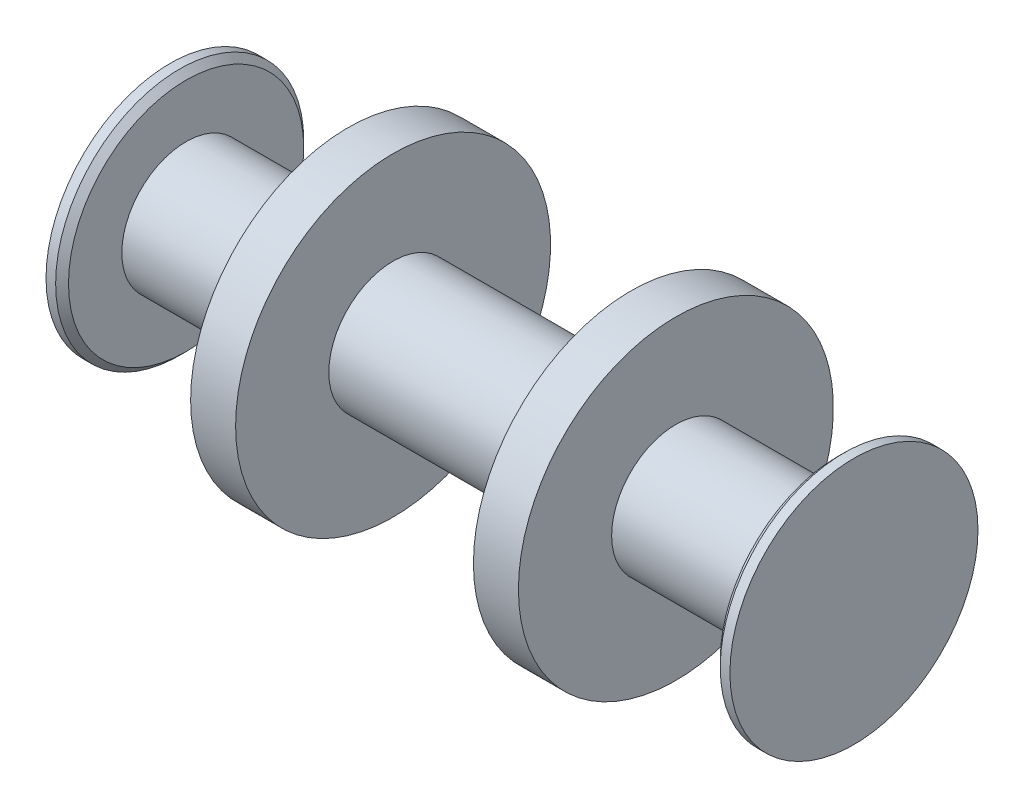
SolidWorks part; units mm, degrees
ref_plane "Front Plane" through (0, 0, 0) normal (0, 0, 1) x (1, 0, 0)
ref_plane "Top Plane" through (0, 0, 0) normal (0, 1, 0) x (1, 0, 0)
ref_plane "Right Plane" through (0, 0, 0) normal (1, 0, 0) x (0, 0, -1)
sketch "Sketch1" plane through (0, 0, 0) normal (0, 0, 1) x (1, 0, 0)
  line L0 (-135.128, 0) -> (0, 0) construction
  line L1 (-135.128, 0) -> (-135.128, 49.022)
  line L2 (-135.128, 49.022) -> (-131.318, 49.022)
  line L4 (-128.778, 46.482) -> (-128.778, 25.4)
  line L5 (-128.778, 25.4) -> (-64.77, 25.4)
  line L7 (-46.99, 25.4) -> (46.99, 25.4)
  line L8 (0, 56.2224) -> (0, -5.4224) construction
  line L9 (-135.128, 0) -> (135.128, 0)
  line L10 (0, 0) -> (0, 25.4)
  line L11 (-131.318, 49.022) -> (-128.778, 46.482)
  line L18 (-64.77, 25.4) -> (-64.77, 62.23)
  line L19 (-64.77, 62.23) -> (-46.99, 62.23)
  line L20 (-46.99, 62.23) -> (-46.99, 25.4)
  line L21 (0, 0) -> (11.2009, 0) construction
  line L22 (46.99, 62.23) -> (46.99, 25.4)
  line L23 (64.77, 62.23) -> (46.99, 62.23)
  line L24 (64.77, 25.4) -> (64.77, 62.23)
  line L25 (128.778, 25.4) -> (64.77, 25.4)
  line L26 (128.778, 46.482) -> (128.778, 25.4)
  line L27 (131.318, 49.022) -> (128.778, 46.482)
  line L28 (135.128, 49.022) -> (131.318, 49.022)
  line L29 (135.128, 0) -> (135.128, 49.022)
  point P5 (-128.778, 49.022)
  point P7 (5.318, 0)
  point P18 (-1.852, 1.8427)
  point P19 (0.1071, 0)
  point P28 (-137.418, 49.022)
  point P29 (-133.0882, 49.022)
  dimension "D1" = 135.128
  dimension "D2" = 49.022
  dimension "D3" = 64.77
  dimension "D4" = 25.4
  dimension "D5" = 6.35
  dimension "D9" = 2.54
  dimension "D10" = 2.54
  dimension "D6" = 36.83
  dimension "D7" = 17.78
  dimension "D8" = 25.4
revolve "Revolve1" add sketch "Sketch1" angle 360 about L0
